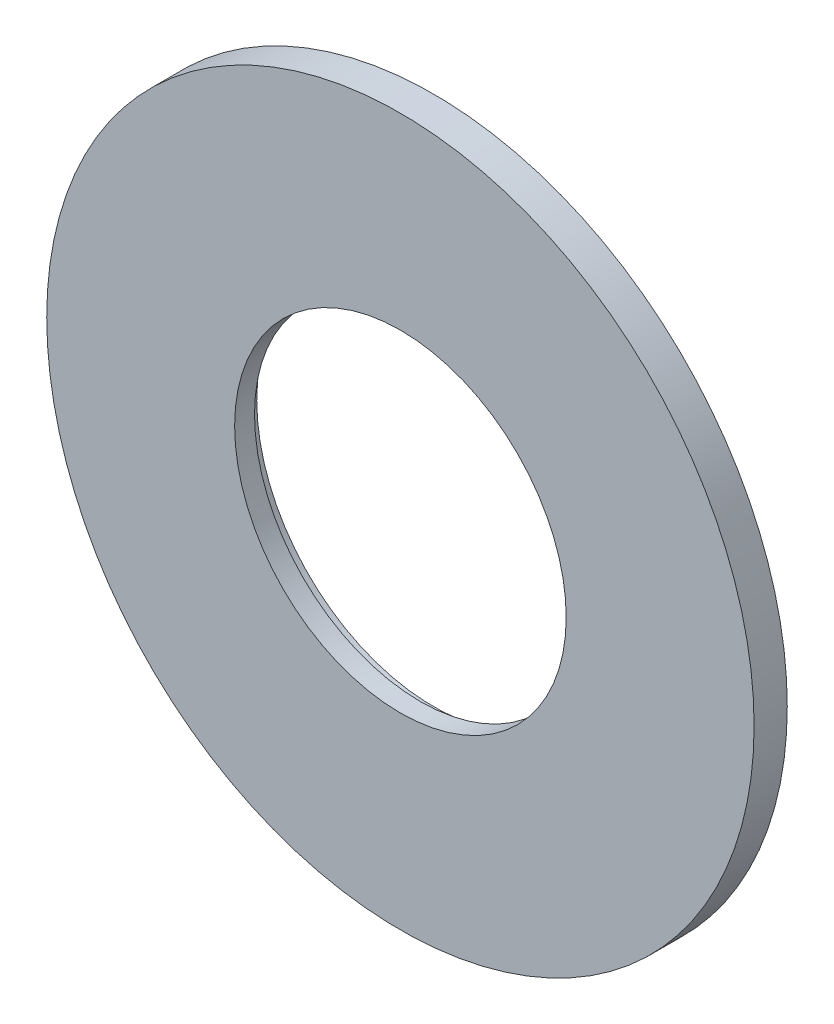
SolidWorks part; units mm, degrees
ref_plane "Piano frontale" through (0, 0, 0) normal (0, 0, 1) x (1, 0, 0)
ref_plane "Piano superiore" through (0, 0, 0) normal (0, 1, 0) x (1, 0, 0)
ref_plane "Piano destro" through (0, 0, 0) normal (1, 0, 0) x (0, 0, -1)
sketch "Schizzo1" plane through (0, 0, 0) normal (0, 0, 1) x (1, 0, 0)
  circle A0 centre (0, 0) radius 16
  circle A1 centre (0, 0) radius 8
  dimension "D1" = 32
  dimension "D2" = 16
extrude "Estrusione-Estrusione1" add sketch "Schizzo1" along normal blind 0.6
sketch "Schizzo3" plane through (0, 0, 0.6) normal (0, 0, 1) x (1, 0, 0)
  circle A0 centre (0, 0) radius 7.5
  circle A1 centre (0, 0) radius 16
  dimension "D1" = 15
extrude "Estrusione-Estrusione2" add sketch "Schizzo3" along normal blind 0.9
sketch "Schizzo5" plane through (0, 0, 0) normal (0, 0, -1) x (-1, 0, 0)
  circle A0 centre (0, 12.5) radius 1.45
  dimension "D1" = 2.9
  dimension "D2" = 12.5
extrude "Estrusione-Estrusione3" add sketch "Schizzo5" along normal blind 1
pattern_circular "RipetizioneCircolare1" count 4 over 360 about axis through (0, 0, 0) along (0, 0, 1) of "Estrusione-Estrusione3"
